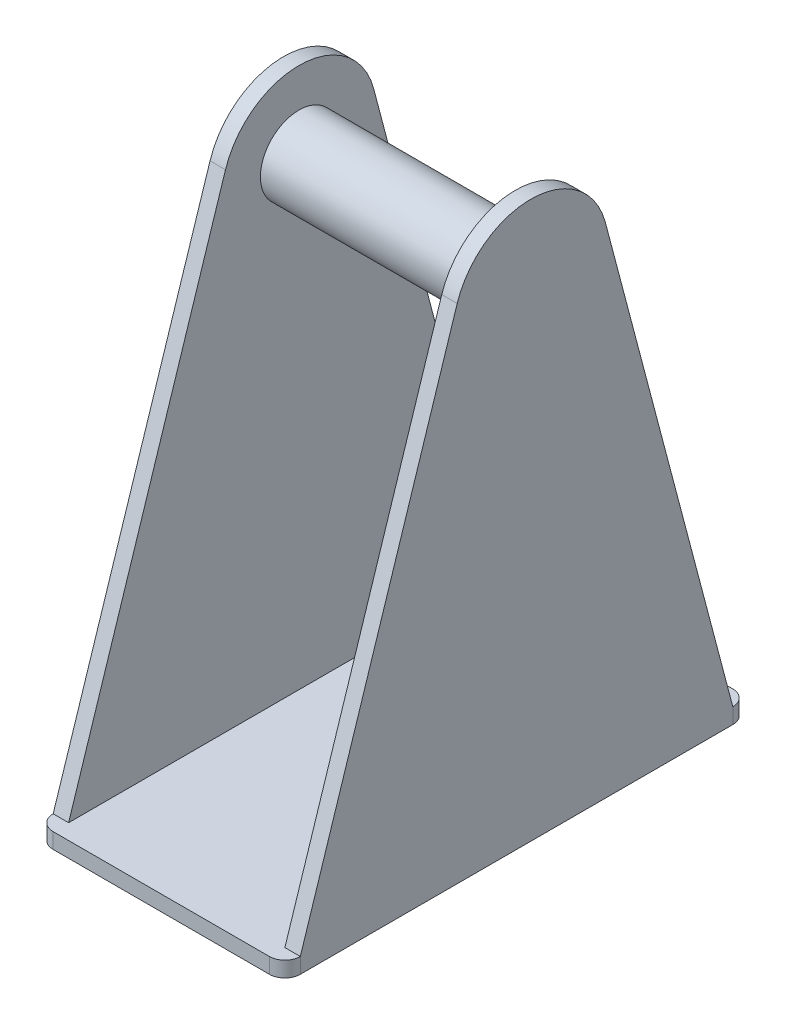
SolidWorks part; units mm, degrees
ref_plane "前视基准面" through (0, 0, 0) normal (0, 0, 1) x (1, 0, 0)
ref_plane "上视基准面" through (0, 0, 0) normal (0, 1, 0) x (1, 0, 0)
ref_plane "右视基准面" through (0, 0, 0) normal (1, 0, 0) x (0, 0, -1)
sketch "草图1" plane through (0, 0, 0) normal (0, 1, 0) x (1, 0, 0)
  line L0 (0, -16.5) -> (0, 16.5) construction
  line L1 (-7, 15) -> (7, 15)
  line L2 (-8, 14) -> (-8, -14)
  line L3 (-7, -15) -> (7, -15)
  line L4 (8, 14) -> (8, -14)
  line L5 (-8.25, 0) -> (8.25, 0) construction
  arc A0 (-8, -14) -> (-7, -15) centre (-7, -14) ccw
  arc A1 (7, -15) -> (8, -14) centre (7, -14) ccw
  arc A2 (8, 14) -> (7, 15) centre (7, 14) ccw
  arc A3 (-8, 14) -> (-7, 15) centre (-7, 14) cw
  dimension "D5" = 1
  dimension "D1" = 8
  dimension "D2" = 8
  dimension "D3" = 15
  dimension "D4" = 15
extrude "凸台-拉伸1" add sketch "草图1" along normal blind 1
sketch "草图2" plane through (-8, 0, 0) normal (-1, 0, 0) x (0, 0, 1)
  line L0 (14, 1) -> (3.8448, 32.5327)
  line L1 (-5.7491, 32.2754) -> (-14, 1)
  line L6 (-14, 0) -> (14, 0)
  line L7 (14, 0) -> (14, 1)
  line L8 (14, 1) -> (-14, 1)
  line L9 (-14, 1) -> (-14, 0)
  line L12 (14, 1) -> (-14, 1)
  arc A0 (3.8448, 32.5327) -> (-5.7491, 32.2754) centre (-0.9145, 31) ccw
  point P7 (0, 4.6729)
  point P10 (-0.2371, 9.0187)
  point P11 (-0.9498, 14.8557)
  dimension "D1" = 10
  dimension "D3" = 30
  dimension "D2" = 0
extrude "凸台-拉伸2" add sketch "草图2" against normal blind 1
mirror "镜向1" about plane through (0, 0, 0) normal (1, 0, 0) of "凸台-拉伸2"
sketch "草图3" plane through (-7, 0, 0) normal (1, 0, 0) x (0, 0, -1)
  circle A0 centre (0.9145, 31) radius 2.5
  dimension "D1" = 5
extrude "凸台-拉伸3" add sketch "草图3" along normal up to next
